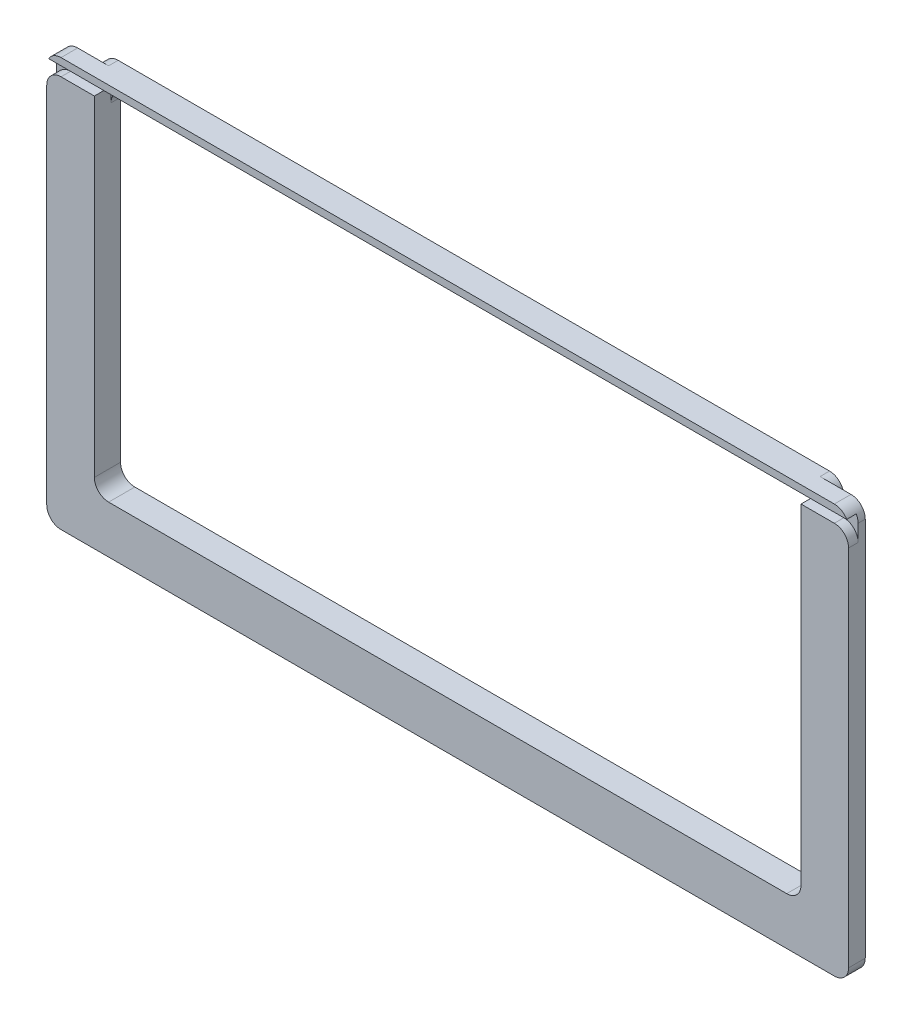
SolidWorks part; units mm, degrees
ref_plane "Front Plane" through (0, 0, 0) normal (0, 0, 1) x (1, 0, 0)
ref_plane "Top Plane" through (0, 0, 0) normal (0, 1, 0) x (1, 0, 0)
ref_plane "Right Plane" through (0, 0, 0) normal (1, 0, 0) x (0, 0, -1)
sketch "Sketch1" plane through (0, 0, 0) normal (0, 0, 1) x (1, 0, 0)
  line L1 (84.245, 42.95) -> (-84.245, 42.95)
  line L2 (84.245, 42.95) -> (84.245, -42.95)
  line L3 (84.245, -42.95) -> (-84.245, -42.95)
  line L4 (-84.245, 42.95) -> (-84.245, -42.95)
  line L5 (84.245, 42.95) -> (-84.245, -42.95) construction
  line L6 (84.245, -42.95) -> (-84.245, 42.95) construction
  point P0 (0, 0)
  dimension "D1" = 168.49
  dimension "D2" = 85.9
extrude "Boss-Extrude1" add sketch "Sketch1" along normal blind 3.5
sketch "Sketch2" plane through (0, 0, 3.5) normal (0, 0, 1) x (1, 0, 0)
  line L0 (84.245, 42.95) -> (-84.245, 42.95) construction
  line L1 (-74.245, 42.95) -> (74.245, 42.95)
  line L2 (-74.245, 42.95) -> (-74.245, -32.95)
  line L3 (-74.245, -32.95) -> (74.245, -32.95)
  line L4 (74.245, 42.95) -> (74.245, -32.95)
  line L5 (-84.245, 42.95) -> (-84.245, -42.95) construction
  line L6 (84.245, -42.95) -> (84.245, 42.95) construction
  line L7 (-84.245, -42.95) -> (84.245, -42.95) construction
  dimension "D1" = 10
  dimension "D2" = 10
  dimension "D3" = 10
extrude "Cut-Extrude1" cut sketch "Sketch2" against normal blind 3.5
sketch "Sketch4" plane through (74.245, 0, 0) normal (-1, 0, 0) x (0, 0, 1)
  line L0 (0, 42.95) -> (0, -42.95) construction
  line L1 (3.5, 42.95) -> (0, 42.95)
  line L2 (3.5, 42.95) -> (3.5, 41.45)
  line L3 (3.5, 41.45) -> (0, 41.45)
  line L4 (0, 42.95) -> (0, 41.45)
  dimension "D1" = 1.5
extrude "Boss-Extrude2" add sketch "Sketch4" along normal up to surface (148.49 mm away) up to face at (-74.245, 5, 1.75)
sketch "Sketch5" plane through (84.245, 0, 0) normal (1, 0, 0) x (0, 0, -1)
  line L0 (-3.5, -42.95) -> (-3.5, 42.95) construction
  line L1 (-3.5, 39.45) -> (-1.5, 39.45)
  line L2 (-3.5, 39.45) -> (-3.5, 41.45)
  line L3 (-3.5, 41.45) -> (-1.5, 41.45)
  line L6 (-3.5, 42.95) -> (0, 42.95) construction
  line L7 (-1.5, 41.45) -> (-1.5, 39.45)
  point P10 (-1.75, 42.95)
  dimension "D1" = 3.5
  dimension "D2" = 1.5
  dimension "D4" = 2
extrude "Cut-Extrude2" cut sketch "Sketch5" against normal blind 176.5
fillet "Fillet3" radius 3 1 edges at (-84.245, -42.95, 1.75)
fillet "Fillet4" radius 3 2 edges at (84.245, -42.95, 1.75) (-84.245, 39.45, 2.5)
sketch "Sketch6" plane through (0, 0, 0) normal (0, 0, -1) x (-1, 0, 0)
  line L12 (-84.245, 42.95) -> (84.245, 42.95) construction
  line L13 (-77.745, 42.95) -> (77.745, 42.95)
  line L14 (-77.745, 42.95) -> (-77.745, -36.45)
  line L15 (-77.745, -36.45) -> (77.745, -36.45)
  line L16 (77.745, 42.95) -> (77.745, -36.45)
  line L17 (-74.245, -32.95) -> (-74.245, 41.45) construction
  line L18 (74.245, -32.95) -> (-74.245, -32.95) construction
  line L19 (74.245, 41.45) -> (74.245, -32.95) construction
  line L20 (-74.245, 39.45) -> (-74.245, -32.95)
  line L21 (-74.245, -32.95) -> (74.245, -32.95)
  line L22 (74.245, 39.45) -> (74.245, -32.95)
  line L23 (-74.245, 39.45) -> (74.245, 39.45)
  dimension "D1" = 3.5
  dimension "D2" = 3.5
  dimension "D3" = 3.5
  dimension "D4" = 3.5
extrude "Boss-Extrude3" add sketch "Sketch6" along normal blind 2
fillet "Fillet5" radius 3 1 edges at (84.245, 39.45, 2.5)
fillet "Fillet6" radius 3 2 edges at (-84.245, 42.95, 1.75) (84.245, 42.95, 1.75)
fillet "Fillet7" radius 3 4 edges at (77.745, 42.95, -1) (-77.745, 42.95, -1) (-77.745, -36.45, -1) (77.745, -36.45, -1)
fillet "Fillet8" radius 3 4 edges at (-74.245, 39.45, -1) (-74.245, -32.95, 0.75) (74.245, -32.95, 0.75) (74.245, 39.45, -1)
